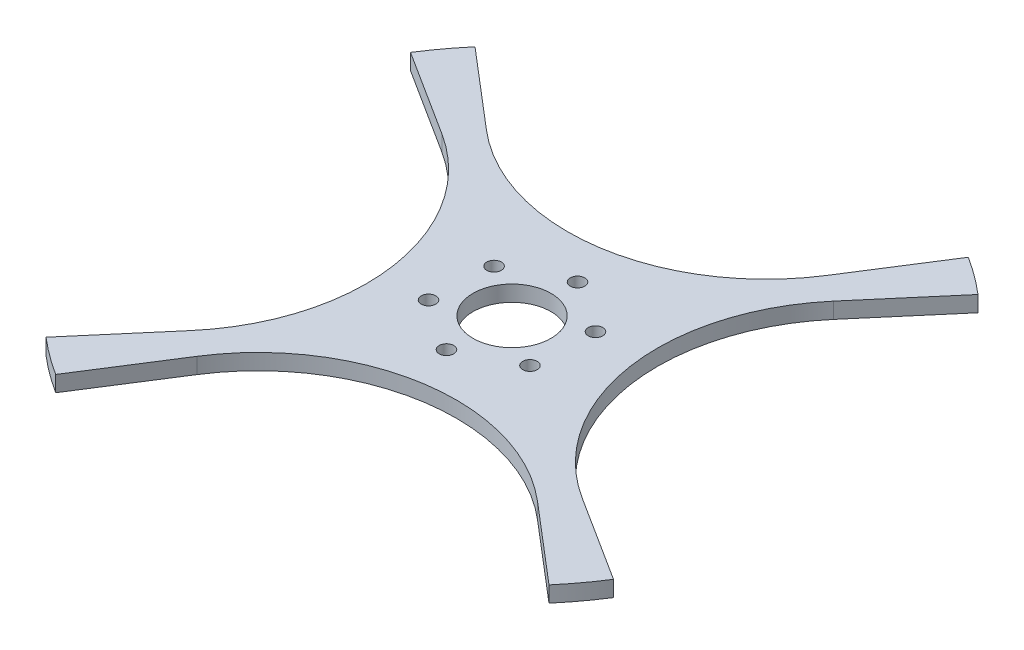
SolidWorks part; units mm, degrees
ref_plane "Front Plane" through (0, 0, 0) normal (0, 0, 1) x (1, 0, 0)
ref_plane "Top Plane" through (0, 0, 0) normal (0, 1, 0) x (1, 0, 0)
ref_plane "Right Plane" through (0, 0, 0) normal (1, 0, 0) x (0, 0, -1)
sketch "Sketch1" plane through (0, 0, 0) normal (0, 1, 0) x (1, 0, 0)
  circle A0 centre (0, 0) radius 125
  circle A6 centre (0, 0) radius 14.75
  dimension "D1" = 250
  dimension "D2" = 29.5
extrude "Boss-Extrude1" add sketch "Sketch1" along normal blind 6
sketch "Sketch2" plane through (0, 6, 0) normal (0, 1, 0) x (1, 0, 0)
  line L0 (-46.3066, -72.7979) -> (-67.0895, -105.4704)
  line L1 (65.6448, -55.9874) -> (95.1069, -81.1152)
  line L4 (95.1069, -142.6966) -> (95.1069, -81.1152)
  line L6 (0, 0) -> (-67.0895, -105.4704) construction
  line L7 (0, 0) -> (95.1069, -81.1152) construction
  line L8 (-67.0895, -105.4704) -> (-67.0895, -164.9292)
  line L9 (-67.0895, -164.9292) -> (95.1069, -142.6966)
  arc A0 (65.6448, -55.9874) -> (-46.3066, -72.7979) centre (16.9756, -113.0516) ccw
  circle A1 centre (0, 0) radius 125 construction
  point P3 (0, 0)
  dimension "D1" = 75
  dimension "D2" = 82
extrude "Cut-Extrude1" cut sketch "Sketch2" against normal blind 6
pattern_circular "CirPattern1" count 4 over 360 about axis through (0, 0, 0) along (0, 1, 0) of "Cut-Extrude1"
sketch "Sketch3" plane through (0, 6, 0) normal (0, 1, 0) x (1, 0, 0)
  circle A0 centre (-1.3134, -23.4633) radius 2.75 construction
  circle A1 centre (19.6631, -12.8691) radius 2.75 construction
  circle A2 centre (20.9765, 10.5942) radius 2.75 construction
  circle A3 centre (1.3134, 23.4633) radius 2.75 construction
  circle A4 centre (-19.6631, 12.8691) radius 2.75 construction
  circle A5 centre (-20.9765, -10.5942) radius 2.75 construction
  circle A6 centre (-1.3134, -23.4633) radius 2.75
  circle A7 centre (19.6631, -12.8691) radius 2.75
  circle A8 centre (20.9765, 10.5942) radius 2.75
  circle A9 centre (1.3134, 23.4633) radius 2.75
  circle A10 centre (-19.6631, 12.8691) radius 2.75
  circle A11 centre (-20.9765, -10.5942) radius 2.75
extrude "Cut-Extrude2" cut sketch "Sketch3" against normal blind 10
